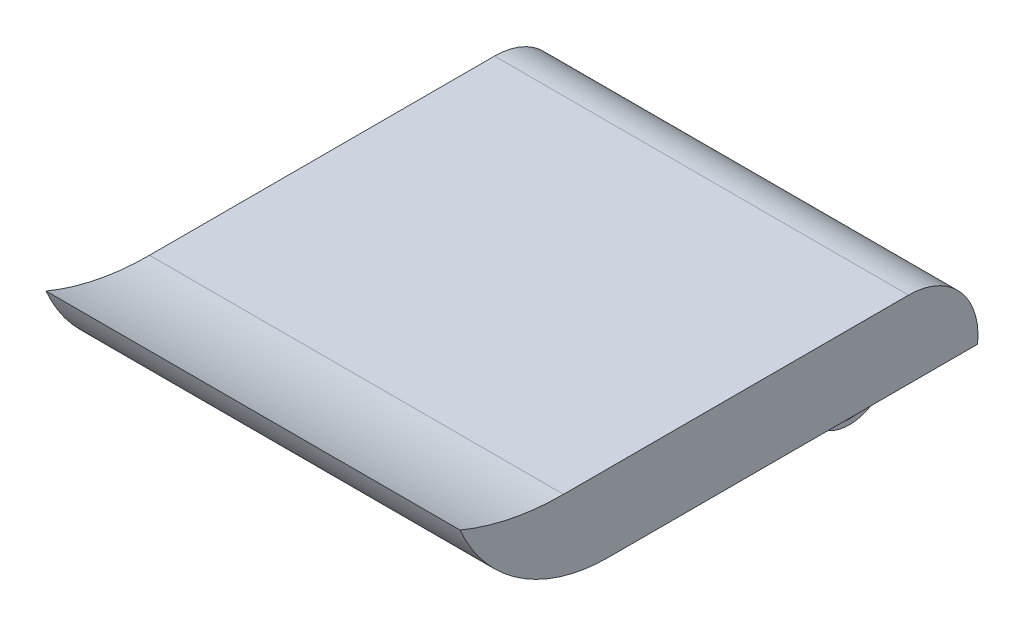
SolidWorks part; units mm, degrees
ref_plane "Front Plane" through (0, 0, 0) normal (0, 0, 1) x (1, 0, 0)
ref_plane "Top Plane" through (0, 0, 0) normal (0, 1, 0) x (1, 0, 0)
ref_plane "Right Plane" through (0, 0, 0) normal (1, 0, 0) x (0, 0, -1)
sketch "Sketch1" plane through (0, 0, 0) normal (1, 0, 0) x (0, 0, -1)
  line L0 (-13.6058, 0) -> (18.4942, 0)
  line L1 (-17.5058, 6.7) -> (12.4942, 6.7)
  arc A0 (-13.6058, 0) -> (-26.5058, 8.51) centre (-13.6058, 14.0323) cw
  arc A1 (-17.5058, 6.7) -> (-26.5058, 8.51) centre (-17.5058, 29.9807) cw
  arc A2 (12.4942, 6.7) -> (18.4942, 0) centre (12.4942, 0.6634) cw
  dimension "D1" = 32.1
  dimension "D2" = 6.7
  dimension "D3" = 45
  dimension "D4" = 26.5058
  dimension "D5" = 6
  dimension "D6" = 9
  dimension "D7" = 1.81
extrude "Boss-Extrude1" add sketch "Sketch1" along normal mid plane 36
sketch "Sketch2" plane through (0, 0, 0) normal (0, -1, 0) x (1, 0, 0)
  line L0 (18, -18.4942) -> (-18, -18.4942) construction
  line L1 (-10.5, -11.1942) -> (10.5, -11.1942)
  line L2 (-10.5, -11.1942) -> (-10.5, -18.4942)
  line L3 (-10.5, -18.4942) -> (10.5, -18.4942)
  line L4 (10.5, -11.1942) -> (10.5, -18.4942)
  line L5 (-10.5, -11.1942) -> (10.5, -18.4942) construction
  line L6 (-10.5, -18.4942) -> (10.5, -11.1942) construction
  point P0 (0, -14.8442)
  dimension "D1" = 21
  dimension "D2" = 7.3
extrude "Boss-Extrude2" add sketch "Sketch2" along normal blind 8
sketch "Sketch3" plane through (-10.5, 0, 0) normal (-1, 0, 0) x (0, 0, 1)
  line L0 (-11.1942, -8) -> (-18.4942, -8) construction
  line L1 (-11.1942, -8) -> (-11.1942, 0) construction
  line L2 (-18.4942, -8) -> (-18.4942, 0) construction
  line L3 (-18.4942, -8) -> (-18.4942, -4.35)
  line L4 (-11.1942, -8) -> (-18.4942, -8)
  line L5 (-11.1942, -8) -> (-11.1942, -4.35)
  arc A0 (-18.4942, -4.35) -> (-11.1942, -4.35) centre (-14.8442, -4.35) ccw
  line M2 (-18.4942, 0) -> (-18.4942, -8)
  line M3 (-18.4942, -8) -> (-11.1942, -8)
  line M4 (-11.1942, -8) -> (-11.1942, 0)
extrude "Cut-Extrude1" cut sketch "Sketch3" against normal through all contours A0 M2 M3 | A0 L4 M4
sketch "Sketch4" plane through (10.5, 0, 0) normal (1, 0, 0) x (0, 0, -1)
  circle A0 centre (14.8442, -5.55) radius 2
  arc A1 (11.1942, -4.35) -> (18.4942, -4.35) centre (14.8442, -4.35) ccw construction
  dimension "D1" = 4
  dimension "D2" = 1.2
  dimension "D3" = 1.2
extrude "Cut-Extrude2" cut sketch "Sketch4" against normal through all
